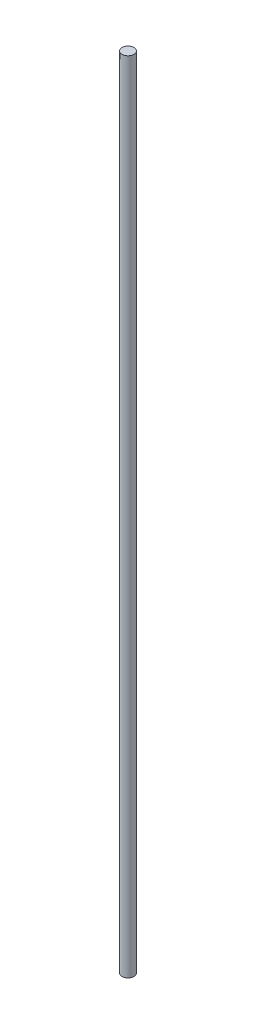
SolidWorks part; units mm, degrees
material "Plain Carbon Steel"
ref_plane "Front Plane" through (0, 0, 0) normal (0, 0, 1) x (1, 0, 0)
ref_plane "Top Plane" through (0, 0, 0) normal (0, 1, 0) x (1, 0, 0)
ref_plane "Right Plane" through (0, 0, 0) normal (1, 0, 0) x (0, 0, -1)
sketch "Sketch1" plane through (0, 0, 0) normal (0, 1, 0) x (1, 0, 0)
  circle A0 centre (0, 0) radius 3
extrude "Boss-Extrude1" add sketch "Sketch1" along normal blind 400
